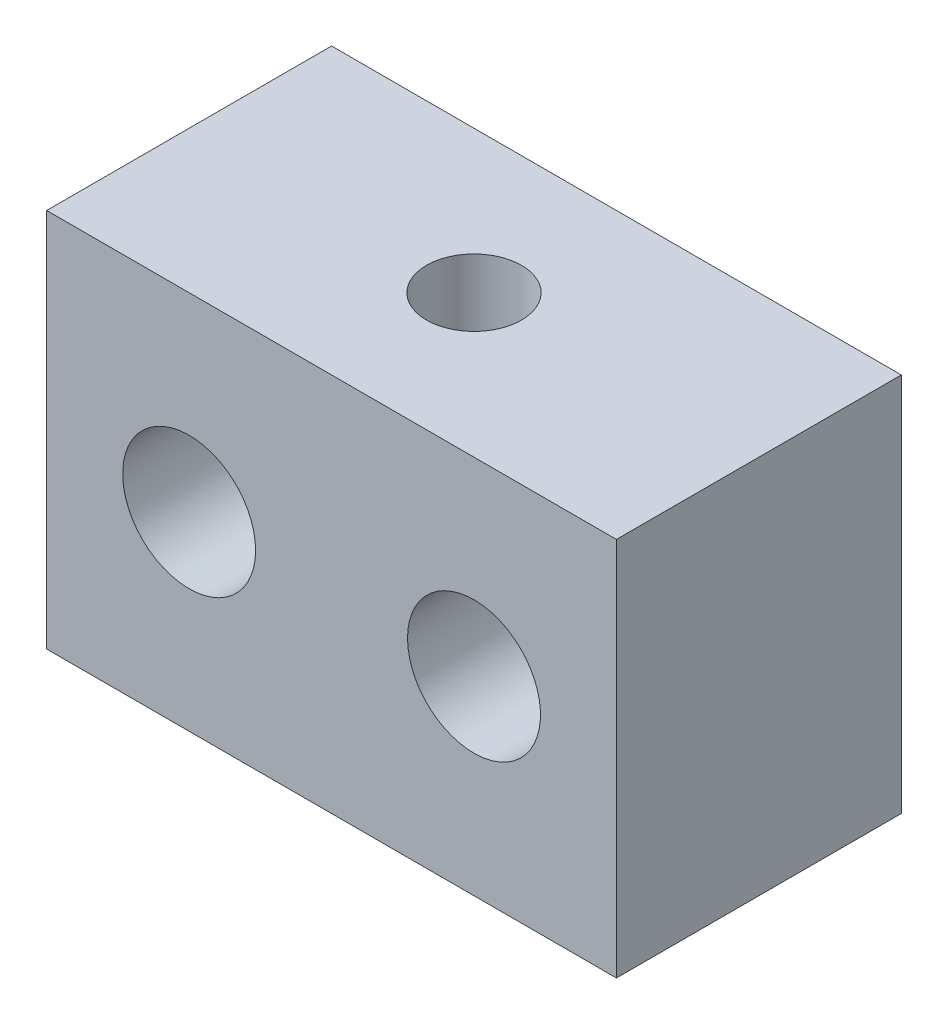
SolidWorks part; units mm, degrees
ref_plane "前视基准面" through (0, 0, 0) normal (0, 0, 1) x (1, 0, 0)
ref_plane "上视基准面" through (0, 0, 0) normal (0, 1, 0) x (1, 0, 0)
ref_plane "右视基准面" through (0, 0, 0) normal (1, 0, 0) x (0, 0, -1)
sketch "草图1" plane through (0, 0, 0) normal (0, 0, 1) x (1, 0, 0)
  line L0 (0, 0) -> (0, 23.9514) construction
  line L1 (-15, 10) -> (15, 10)
  line L2 (-15, 10) -> (-15, -10)
  line L3 (-15, -10) -> (15, -10)
  line L4 (15, 10) -> (15, -10)
  line L5 (-15, 10) -> (15, -10) construction
  line L6 (-15, -10) -> (15, 10) construction
  circle A0 centre (-7.5, 0) radius 3.5
  circle A1 centre (7.5, 0) radius 3.5
  point P0 (0, 0)
  dimension "D3" = 7
  dimension "D1" = 30
  dimension "D2" = 20
  dimension "D4" = 15
  dimension "D5" = 10
extrude "凸台-拉伸1" add sketch "草图1" along normal blind 15
hole_wizard "M6 螺纹孔1" positions "3D草图1" profile "草图2" tap size "M6" standard "GB"
sketch3d "3D草图1"
  line L0 (15, 10, 15) -> (15, 10, 0) construction
  line L1 (15, 10, 0) -> (-15, 10, 0) construction
  point P0 (0, 10, 7.5)
  dimension "D1" = 15
  dimension "D2" = 7.5
sketch "草图2" plane through (0, 10, 7.5) normal (1, 0, 0) x (0, 0, 1)
  line L0 (0, 0) -> (0, 16.5022)
  line L1 (0, 16.5022) -> (2.5, 15)
  line L2 (2.5, 15) -> (2.5, 0)
  line L5 (2.5, 0) -> (0, 0)
  line L10 (0, 16.5022) -> (-2.5, 15) construction
  line L11 (0, -6.35) -> (0, 107.95) construction
  dimension "螺纹孔钻头直径" = 5
  dimension "螺纹孔钻头深度" = 15
  dimension "导头角度" = 118
cosmetic thread "孔螺蚊线1"
